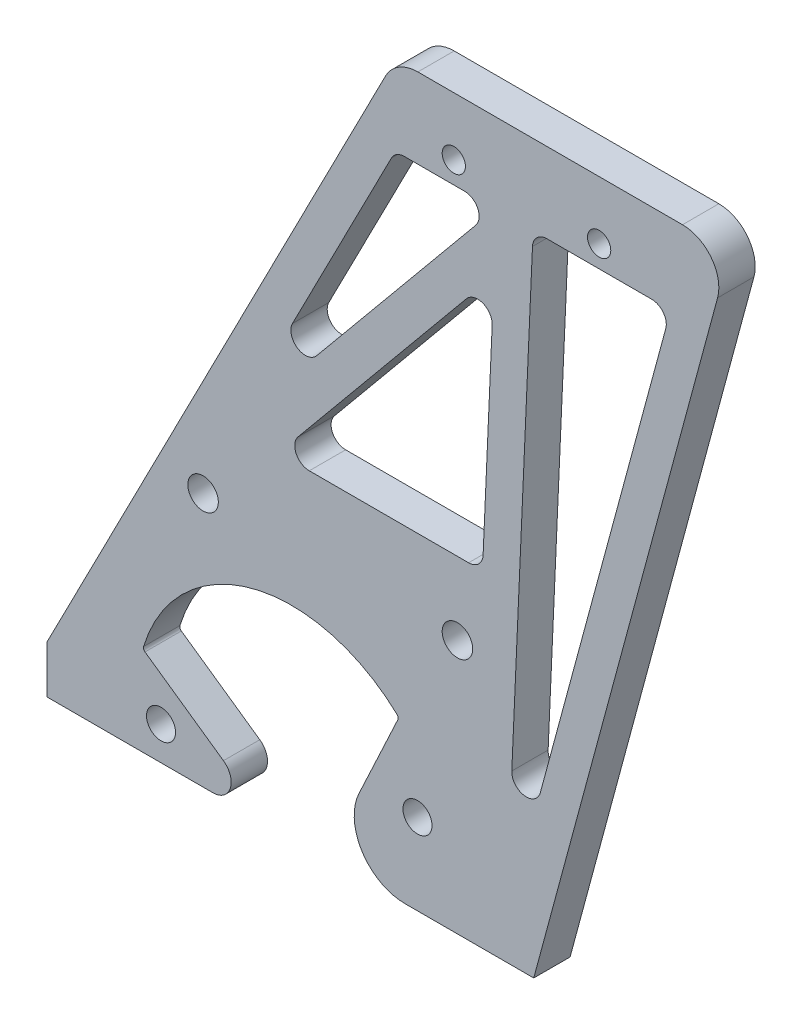
SolidWorks part; units mm, degrees
material "Thornel Mat VMA"
ref_plane "前视基准面" through (0, 0, 0) normal (0, 0, 1) x (1, 0, 0)
ref_plane "上视基准面" through (0, 0, 0) normal (0, 1, 0) x (1, 0, 0)
ref_plane "右视基准面" through (0, 0, 0) normal (1, 0, 0) x (0, 0, -1)
sketch "草图1" plane through (0, 0, 0) normal (0, 0, 1) x (1, 0, 0)
  line L1 (-33.5, 15) -> (33.5, 15)
  line L2 (-33.5, 15) -> (-33.5, -15)
  line L3 (-33.5, -15) -> (33.5, -15)
  line L4 (33.5, 15) -> (33.5, -15)
  line L5 (-33.5, 15) -> (33.5, -15) construction
  line L6 (-33.5, -15) -> (33.5, 15) construction
  point P0 (0, 0)
  dimension "D1" = 30
  dimension "D2" = 67
extrude "凸台-拉伸1" add sketch "草图1" along normal blind 5
sketch "草图3" plane through (0, 0, 5) normal (0, 0, 1) x (1, 0, 0)
  line L0 (0.156, -18.5) -> (0, 0) construction
  line L1 (33.5, -15) -> (33.5, 15) construction
  circle A0 centre (0.156, -18.5) radius 11.5
  dimension "D2" = 23
  dimension "D1" = 18.5
  dimension "D3" = 0.483
extrude "切除-拉伸1" cut sketch "草图3" against normal through all
sketch "草图4" plane through (0, 0, 5) normal (0, 0, 1) x (1, 0, 0)
  line L0 (0.156, -18.5) -> (0.156, 2.75) construction
  line L1 (14.9513, -3.2467) -> (0.156, -34.9754)
  line L2 (-20.2837, -12.6879) -> (0.156, -27)
  line L3 (0.156, -27) -> (0.156, -34.9754)
  arc A0 (14.9513, -3.2467) -> (-20.2837, -12.6879) centre (0.156, -18.5) ccw
  dimension "D1" = 42.5
  dimension "D2" = 18.5
  dimension "D3" = 27
  dimension "D4" = 34.9754
  dimension "D5" = 55
  dimension "D6" = 25
extrude "切除-拉伸2" cut sketch "草图4" against normal blind 5
sketch "草图5" plane through (0, 0, 5) normal (0, 0, 1) x (1, 0, 0)
  line L0 (-16.9818, -15) -> (-2.7003, -25)
  line L1 (-2.7003, -25) -> (-33.5, -25)
  line L2 (-33.5, -25) -> (-33.5, -15)
  line L3 (-20.2837, -12.6879) -> (-16.9818, -15) construction
  line L4 (-33.5, -15) -> (-16.9818, -15)
  line L5 (33.5, -15) -> (33.5, -25)
  line L6 (11.1104, -15) -> (33.5, -15) construction
  line L7 (33.5, -25) -> (4.8076, -25)
  line L8 (4.8076, -25) -> (10.3345, -13.1476)
  line L9 (10.3345, -13.1476) -> (14.9513, -3.2467) construction
  line L10 (33.5, -15) -> (33.5, 15) construction
  line L11 (10.3345, -13.1476) -> (33.5, -15)
  arc A0 (11.1104, -15) -> (10.3345, -13.1476) centre (0.156, -18.5) ccw construction
  dimension "D1" = 10
extrude "凸台-拉伸2" add sketch "草图5" against normal up to surface (5 mm away) up to face at (-0.3896, -5.4524, 0)
fillet "圆角1" radius 2.5 1 edges at (-2.7003, -25, 2.5)
fillet "圆角3" radius 0.5 2 edges at (-20.2837, -12.6879, 2.5) (14.9513, -3.2467, 2.5)
fillet "圆角4" radius 7 1 edges at (4.8076, -25, 2.5)
sketch "草图6" plane through (0, 0, 5) normal (0, 0, 1) x (1, 0, 0)
  line L0 (0.119, -18.5) -> (0, 0) construction
  line L1 (15.7954, -25) -> (33.5, -25) construction
  line L2 (0.119, -18.5) -> (34.657, -18.5) construction
  line L3 (17.5057, -13.8413) -> (0.119, -18.5) construction
  line L4 (-17.7824, -20.3815) -> (0.119, -18.5) construction
  circle A0 centre (0.119, -18.5) radius 18 construction
  circle A1 centre (17.5057, -13.8413) radius 2
  circle A2 centre (-17.7824, -20.3815) radius 2
  dimension "D1" = 36
  dimension "D4" = 4
  dimension "D2" = 90.369
  dimension "D3" = 18.5
  dimension "D5" = 15
  dimension "D6" = 6
extrude "切除-拉伸3" cut sketch "草图6" against normal through all
sketch "草图7" plane through (0, 0, 5) normal (0, 0, 1) x (1, 0, 0)
  line L0 (60.5, 75) -> (14.5, 75)
  line L1 (14.5, 75) -> (-16.3038, 15)
  line L4 (33.5, 15) -> (-33.5, 15) construction
  line L5 (33.5, 15) -> (60.5, 75)
  line L6 (33.5, 15) -> (-16.3038, 15)
  dimension "D1" = 49.8038
  dimension "D2" = 46
  dimension "D3" = 75
  dimension "D4" = 60.5
  dimension "D5" = 33.5
extrude "凸台-拉伸3" add sketch "草图7" against normal up to surface (5 mm away) up to face at (19.5057, -13.8413, 0)
sketch "草图8" plane through (0, 0, 5) normal (0, 0, 1) x (1, 0, 0)
  line L0 (-16.3038, 15) -> (-33.5, -18.495)
  line L1 (-33.5, 15) -> (-33.5, -25) construction
  line L2 (14.5, 75) -> (-16.3038, 15) construction
  line L3 (-33.5, 15) -> (-16.3038, 15)
  line L4 (-33.5, -18.495) -> (-33.5, 15)
extrude "切除-拉伸4" cut sketch "草图8" against normal through all
sketch "草图9" plane through (0, 0, 5) normal (0, 0, 1) x (1, 0, 0)
  line L0 (60.5, 75) -> (33.5, -25)
  line L1 (33.5, -25) -> (33.5, 15)
  line L2 (33.5, 15) -> (60.5, 75)
extrude "凸台-拉伸4" add sketch "草图9" against normal up to surface (5 mm away) up to face at (19.5057, -13.8413, 0)
sketch "草图10" plane through (0, 0, 5) normal (0, 0, 1) x (1, 0, 0)
  line L0 (-12, 10) -> (23, 10) construction
  circle A0 centre (-12, 10) radius 2.1
  circle A1 centre (23, 10) radius 2.1
  dimension "D2" = 4.2
  dimension "D1" = 10
  dimension "D3" = 12
  dimension "D4" = 35
extrude "切除-拉伸5" cut sketch "草图10" against normal through all
fillet "圆角5" radius 5 2 edges at (60.5, 75, 2.5) (14.5, 75, 2.5)
sketch "草图11" plane through (0, 0, 5) normal (0, 0, 1) x (1, 0, 0)
  line L0 (22.5, 67) -> (42.5, 67) construction
  line L1 (53.971, 75) -> (17.5535, 75) construction
  circle A0 centre (42.5, 67) radius 1.6
  circle A1 centre (22.5, 67) radius 1.6
  dimension "D3" = 3.2
  dimension "D1" = 8
  dimension "D2" = 20
  dimension "D4" = 22.5
extrude "切除-拉伸6" cut sketch "草图11" against normal through all
sketch "草图12" plane through (0, 0, 5) normal (0, 0, 1) x (1, 0, 0)
  line L16 (-8.1164, 20) -> (31.4524, 20)
  line L17 (14.4731, 64) -> (52.351, 64)
  line L18 (33.412, 64) -> (29.671, -20)
  line L19 (28.417, 64.2225) -> (24.6759, -19.7775)
  line L20 (28.417, 64.2225) -> (-8.1164, 20)
  line L21 (32.2717, 61.038) -> (-4.2616, 16.8155)
  line L24 (29.671, -20) -> (53.971, 70)
  line L25 (53.971, 70) -> (17.5535, 70)
  line L26 (17.5535, 70) -> (-18.2976, 0.1689)
  line L27 (19.3311, -5.6852) -> (13.9828, -17.1548)
  line L28 (15.7954, -20) -> (29.671, -20)
  line L29 (29.671, -20) -> (53.971, 70)
  line L30 (53.971, 70) -> (17.5535, 70)
  line L31 (17.5535, 70) -> (-18.2976, 0.1689)
  line L32 (19.3311, -5.6852) -> (13.9828, -17.1548)
  line L33 (15.7954, -20) -> (29.671, -20)
  arc A21 (18.1077, 0.652) -> (-18.2976, 0.1689) centre (0.156, -18.5) ccw
  arc A22 (19.3311, -5.6852) -> (18.1077, 0.652) centre (14.3464, -3.3608) ccw
  arc A23 (13.9828, -17.1548) -> (15.7954, -20) centre (15.7954, -18) ccw
  arc A24 (18.1077, 0.652) -> (-18.2976, 0.1689) centre (0.156, -18.5) ccw
  arc A25 (19.3311, -5.6852) -> (18.1077, 0.652) centre (14.3464, -3.3608) ccw
  arc A26 (13.9828, -17.1548) -> (15.7954, -20) centre (15.7954, -18) ccw
  dimension "D2" = 40
  dimension "D3" = 6
  dimension "D1" = 5
  dimension "D4" = 5
  dimension "D5" = 5
extrude "切除-拉伸7" cut sketch "草图12" against normal blind 10 contours L18 L29 L17 | L19 L21 L16 | L17 L31 L20
fillet "圆角6" radius 2 9 edges at (28.2332, 64, 2.5) (-8.1164, 20, 2.5) (14.4731, 64, 2.5) (26.4475, 20, 2.5) (-1.6308, 20, 2.5) (28.0474, 55.9246, 2.5) (33.412, 64, 2.5) (52.351, 64, 2.5) (29.671, -20, 2.5)
